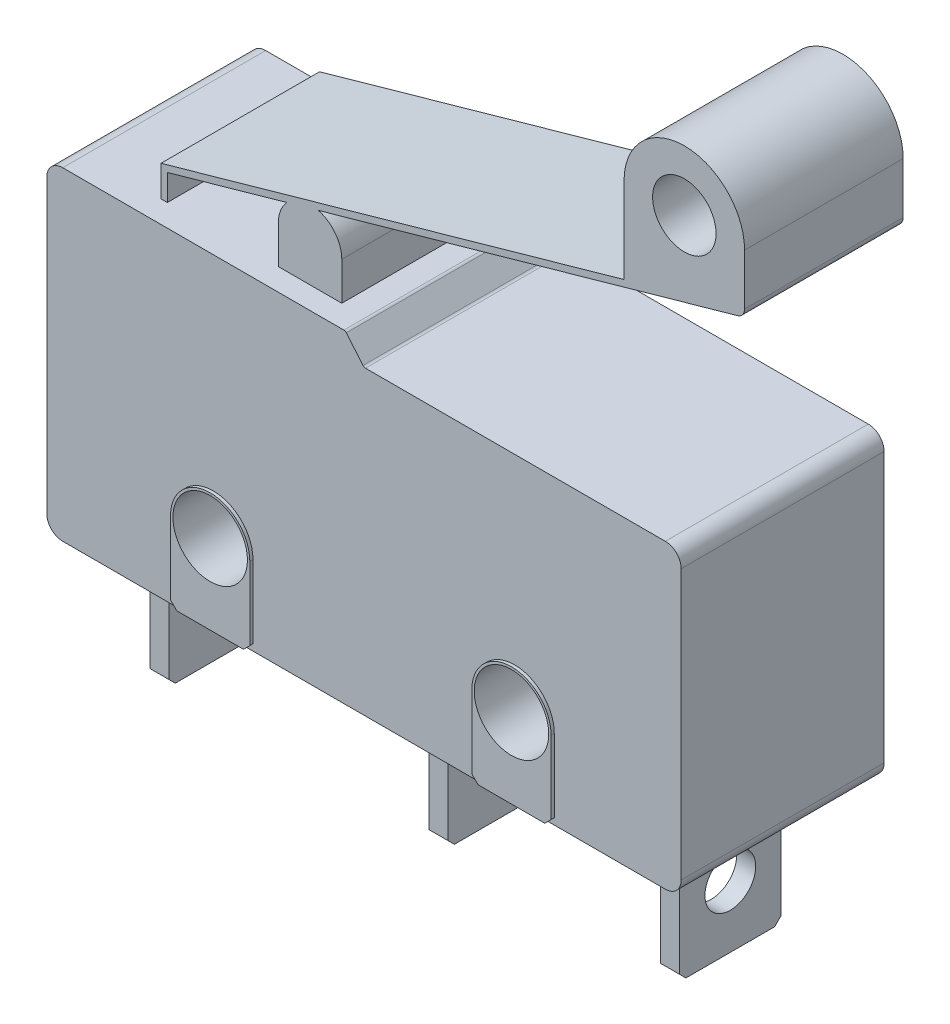
SolidWorks part; units mm, degrees
ref_plane "前视基准面" through (0, 0, 0) normal (0, 0, 1) x (1, 0, 0)
ref_plane "上视基准面" through (0, 0, 0) normal (0, 1, 0) x (1, 0, 0)
ref_plane "右视基准面" through (0, 0, 0) normal (1, 0, 0) x (0, 0, -1)
sketch "草图1" plane through (0, 0, 0) normal (0, 0, 1) x (1, 0, 0)
  line L0 (10, 0) -> (10, 10.2) construction
  line L1 (0, 0) -> (20, 0)
  line L2 (0, 0) -> (0, 10.2)
  line L3 (0, 10.2) -> (20, 10.2)
  line L4 (20, 0) -> (20, 10.2)
  circle A0 centre (5.25, 2.5) radius 1.175
  circle A1 centre (14.75, 2.5) radius 1.175
  dimension "D3" = 2.35
  dimension "D5" = 2.5
  dimension "D7" = 9.5
  dimension "D1" = 20
  dimension "D2" = 10.2
extrude "凸台-拉伸1" add sketch "草图1" along normal blind 6.4
ref_plane "基准面1" through (0, 0, 3.2) normal (0, 0, 1) x (1, 0, 0)
sketch "草图7" plane through (0, 0, 6.4) normal (0, 0, 1) x (1, 0, 0)
  line L0 (20, 9.5) -> (10, 9.5)
  line L1 (20, 0) -> (20, 10.2) construction
  line L2 (10, 9.5) -> (9.4126, 10.2)
  line L3 (20, 10.2) -> (0, 10.2) construction
  line L4 (9.4126, 10.2) -> (20, 10.2)
  line L5 (20, 10.2) -> (20, 9.5)
  line L6 (0, 0) -> (20, 0) construction
  dimension "D1" = 9.5
  dimension "D2" = 10
  dimension "D3" = 130
extrude "切除-拉伸1" cut sketch "草图7" against normal through all both and the other way through all
fillet "圆角1" radius 0.1 2 edges at (10, 9.5, 3.2) (9.4126, 10.2, 3.2)
fillet "圆角2" radius 0.5 4 edges at (20, 0, 3.2) (0, 0, 3.2) (0, 10.2, 3.2) (20, 9.5, 3.2)
sketch "草图8" plane through (0, 0, 6.4) normal (0, 0, 1) x (1, 0, 0)
  line L0 (4, 2.5) -> (4, 0)
  line L1 (0.5, 0) -> (19.5, 0) construction
  line L2 (4, 0) -> (6.5, 0)
  line L3 (6.5, 0) -> (6.5, 2.5)
  line L4 (13.5, 2.5) -> (13.5, 0)
  line L5 (13.5, 0) -> (16, 0)
  line L6 (16, 0) -> (16, 2.5)
  arc A0 (6.5, 2.5) -> (4, 2.5) centre (5.25, 2.5) ccw
  arc A1 (16, 2.5) -> (13.5, 2.5) centre (14.75, 2.5) ccw
  circle A2 centre (5.25, 2.5) radius 1.175
  circle A3 centre (14.75, 2.5) radius 1.175
  circle A4 centre (14.75, 2.5) radius 1.175 construction
  circle A5 centre (5.25, 2.5) radius 1.175 construction
  dimension "D1" = 2.5
  dimension "D2" = 2.5
extrude "凸台-拉伸5" add sketch "草图8" along normal blind 0.1
mirror "镜向1" about plane through (0, 0, 3.2) normal (0, 0, 1) of "凸台-拉伸5"
chamfer "倒角1" distance 0.2 angle 45 8 edges at (6.5, 0, 6.45) (4, 0, 6.45) (13.5, 0, 6.45) (16, 0, 6.45) (6.5, 0, -0.05) (4, 0, -0.05) (13.5, 0, -0.05) (16, 0, -0.05)
sketch "草图3" plane through (0, 0, 3.2) normal (0, 0, 1) x (1, 0, 0)
  line L0 (0, 0) -> (20, 0) construction
  line L1 (1.65, 0) -> (2.25, 0)
  line L2 (1.65, 0) -> (1.65, -3.9)
  line L3 (1.65, -3.9) -> (2.25, -3.9)
  line L4 (2.25, 0) -> (2.25, -3.9)
  line L5 (0, 9.7) -> (0, 0.5) construction
  line L6 (10.45, 0) -> (11.05, 0)
  line L7 (10.45, 0) -> (10.45, -3.9)
  line L8 (10.45, -3.9) -> (11.05, -3.9)
  line L9 (11.05, 0) -> (11.05, -3.9)
  line L10 (17.75, 0) -> (18.35, 0)
  line L11 (17.75, 0) -> (17.75, -3.9)
  line L12 (17.75, -3.9) -> (18.35, -3.9)
  line L13 (18.35, 0) -> (18.35, -3.9)
  circle A0 centre (5.25, 2.5) radius 1.175 construction
  dimension "D5" = 6.4
  dimension "D1" = 0.6
  dimension "D2" = 1.65
  dimension "D3" = 8.8
  dimension "D4" = 7.3
extrude "凸台-拉伸2" add sketch "草图3" along normal mid plane 3.2
sketch "草图9" plane through (1.65, 0, 0) normal (-1, 0, 0) x (0, 0, 1)
  line L0 (3.2, -3.9) -> (3.2, 0) construction
  line L1 (4.8, -3.9) -> (1.6, -3.9) construction
  line L2 (4.8, 0) -> (1.6, 0) construction
  line L3 (1.6, -1.95) -> (4.8, -1.95) construction
  line L4 (1.6, 0) -> (1.6, -3.9) construction
  line L5 (4.8, 0) -> (4.8, -3.9) construction
  circle A0 centre (3.2, -1.95) radius 0.8
  dimension "D1" = 1.6
extrude "切除-拉伸2" cut sketch "草图9" against normal through all
chamfer "倒角2" distance 0.2 angle 45 6 edges at (18.05, -3.9, 4.8) (10.75, -3.9, 4.8) (18.05, -3.9, 1.6) (10.75, -3.9, 1.6) (1.95, -3.9, 1.6) (1.95, -3.9, 4.8)
sketch "草图5" plane through (0, 0, 3.2) normal (0, 0, 1) x (1, 0, 0)
  line L0 (3, 10.2) -> (3, 11.0959) construction
  line L1 (9.366, 10.2) -> (0.5, 10.2) construction
  line L2 (3, 11.0959) -> (20.8023, 16.1264) construction
  line L3 (0, 9.7) -> (0, 0.5) construction
  line L4 (21.3, 18) -> (21.3, 16.2671)
  line L5 (3.1, 10.1938) -> (3.1, 11.0202)
  line L6 (3.1, 11.0202) -> (21.3, 16.1632)
  line L7 (2.9, 10.2) -> (2.9, 11.1715)
  line L8 (2.9, 11.1715) -> (17.5, 15.2972)
  line L9 (2.9, 10.2) -> (2.9, 11.1715) construction
  line L10 (17.5, 18) -> (17.5, 15.2972)
  line L11 (21.3, 16.2671) -> (21.3, 16.1632)
  line L12 (2.9, 10.2) -> (3.1, 10.1938)
  line L13 (9.366, 10.2) -> (0.5, 10.2) construction
  line L14 (15.8, 0) -> (19.5, 0) construction
  line L15 (3.1, 10.2) -> (3.1, 11.0202) construction
  line L16 (3.1, 11.0202) -> (20.8295, 16.0302) construction
  line L17 (2.9, 11.1715) -> (20.7751, 16.2227) construction
  line L18 (19.4, 19.9) -> (14.1684, 19.9) construction
  circle A1 centre (19.4, 18) radius 1
  arc A4 (21.3, 18) -> (17.5, 18) centre (19.4, 18) ccw
  dimension "D1" = 18
  dimension "D7" = 2
  dimension "D2" = 16.4
  dimension "D3" = 3
  dimension "D6" = 18.3
  dimension "D4" = 0.1
extrude "凸台-拉伸3" add sketch "草图5" along normal mid plane 5 separate body
sketch "草图6" plane through (0, 0, 3.2) normal (0, 0, 1) x (1, 0, 0)
  line L0 (3, 10.2) -> (3, 11.0959) construction
  line L1 (3, 11.0959) -> (20.8023, 16.1264) construction
  line L2 (20.5793, 18.1312) -> (20.8023, 16.1264)
  line L3 (18.2135, 18) -> (18.2135, 15.4988)
  line L4 (2.9, 10.19) -> (2.9, 11.1715)
  line L5 (2.9, 11.1715) -> (18.2135, 15.4988)
  line L6 (3.1, 10.2) -> (3.1, 11.0202)
  line L7 (3.1, 11.0202) -> (20.8295, 16.0302)
  line L8 (20.8295, 16.0302) -> (20.8023, 16.1264)
  line L9 (2.9, 11.1715) -> (20.7751, 16.2227) construction
  line L10 (2.9, 10.2) -> (2.9, 11.1715) construction
  line L11 (2.9, 10.19) -> (3.1, 10.2)
  arc A0 (20.5793, 18.1312) -> (18.2135, 18) centre (19.4, 18) ccw
  circle A1 centre (19.4, 18) radius 1
  circle A2 centre (19.4, 18) radius 1 construction
  dimension "D1" = 0.1
  dimension "D2" = 0.1
extrude "凸台-拉伸4" [suppressed] add sketch "草图6" along normal mid plane 4.5
sketch "草图10" plane through (0, 0, 3.2) normal (0, 0, 1) x (1, 0, 0)
  line L0 (6.6, 11.4) -> (6.6, 10.2)
  line L1 (9.366, 10.2) -> (0.5, 10.2) construction
  line L2 (6.6, 10.2) -> (8.6, 10.2)
  line L3 (8.6, 10.2) -> (8.6, 11.4)
  arc A0 (8.6, 11.4) -> (6.6, 11.4) centre (7.6, 11.4) ccw
  dimension "D1" = 1
  dimension "D2" = 4.5
  dimension "D3" = 1.2
extrude "凸台-拉伸6" add sketch "草图10" along normal mid plane 5
fillet "圆角3" radius 0.3 1 edges at (21.3, 16.1632, 3.2)
